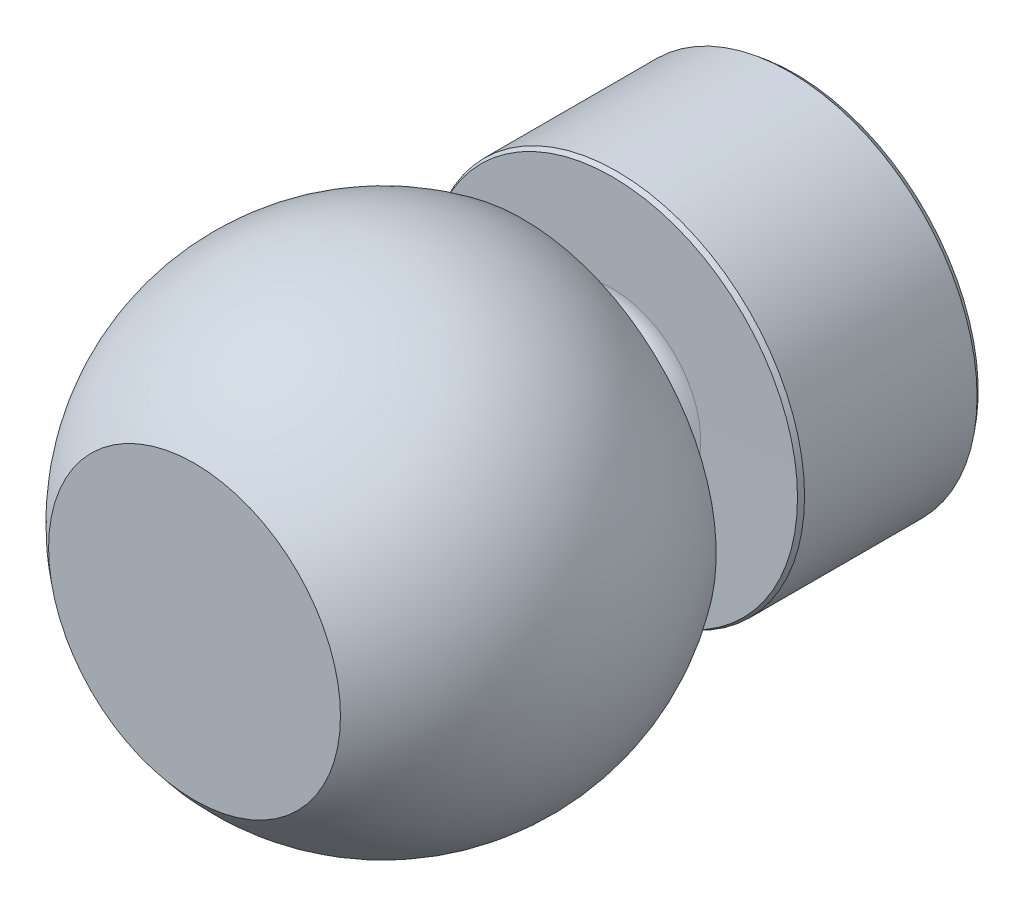
SolidWorks part; units mm, degrees
ref_plane "Front Plane" through (0, 0, 0) normal (0, 0, 1) x (1, 0, 0)
ref_plane "Top Plane" through (0, 0, 0) normal (0, 1, 0) x (1, 0, 0)
ref_plane "Right Plane" through (0, 0, 0) normal (1, 0, 0) x (0, 0, -1)
sketch "Sketch1" plane through (0, 0, 0) normal (0, 1, 0) x (1, 0, 0)
  line L0 (14.122, -2.5299) -> (14.122, -66.5299) construction
  line L1 (18.5542, -2.5299) -> (28.122, -2.5299)
  line L2 (23.5257, -21.9946) -> (33.872, -22.0299)
  line L4 (25.8925, -31.5299) -> (34.7071, -31.5299)
  line L5 (19.0911, -66.5299) -> (29.6723, -66.5299)
  line L6 (34.122, -16.9477) -> (34.122, -21.5299)
  line L7 (34.122, -21.5299) -> (33.872, -22.0299)
  line L9 (21.122, -24.5299) -> (21.122, -29.5299)
  line L10 (23.122, -31.5299) -> (23.1639, -31.5299)
  line L11 (19.0911, -66.5299) -> (14.122, -66.5299)
  line L12 (25.8925, -31.5299) -> (23.1639, -31.5299)
  line L13 (14.122, -2.5299) -> (14.122, -66.5299)
  line L19 (28.122, -2.5299) -> (33.622, -2.5299)
  line L20 (34.122, -16.9477) -> (34.122, -3.1471)
  line L21 (33.622, -2.5299) -> (34.122, -3.1471)
  line L22 (18.5542, -2.5299) -> (14.122, -2.5299)
  arc A0 (23.5257, -21.9946) -> (21.122, -24.5299) centre (23.6609, -24.5299) ccw
  arc A1 (21.122, -29.5299) -> (23.122, -31.5299) centre (23.122, -29.5299) ccw
  arc A4 (29.6723, -66.5299) -> (34.7071, -31.5299) centre (14.122, -46.4308) ccw
  dimension "D3" = 20
revolve "Revolve1" add sketch "Sketch1" angle 360 about L0
ref_point "Center of Ball"
